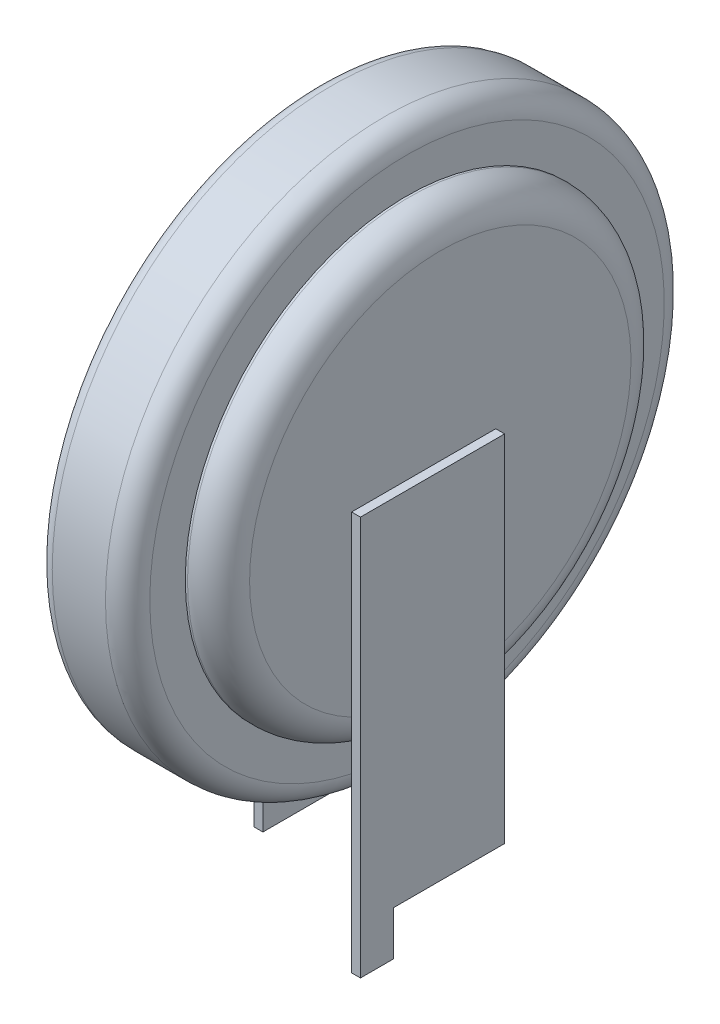
SolidWorks part; units mm, degrees
ref_plane "Front Plane" through (0, 0, 0) normal (0, 0, 1) x (1, 0, 0)
ref_plane "Top Plane" through (0, 0, 0) normal (0, 1, 0) x (1, 0, 0)
ref_plane "Right Plane" through (0, 0, 0) normal (1, 0, 0) x (0, 0, -1)
sketch "Sketch1" plane through (0, 0, 0) normal (0, 0, 1) x (1, 0, 0)
  line L0 (-11.9332, 7.8) -> (5.654, 7.8) construction
  line L1 (0, 0) -> (0, 7.8) construction
  line L2 (-1.375, 7.8) -> (1.375, 7.8)
  line L3 (1.375, 7.8) -> (1.375, 12.1)
  line L4 (0.675, 12.8) -> (0.625, 12.8)
  line L5 (0.625, 12.8) -> (0.625, 13.6)
  line L6 (0.125, 14.1) -> (-1.075, 14.1)
  line L7 (-1.375, 13.8) -> (-1.375, 7.8)
  line L8 (-3.1396, 1.5) -> (8.3283, 1.5) construction
  arc A0 (1.375, 12.1) -> (0.675, 12.8) centre (0.675, 12.1) ccw
  arc A1 (0.125, 14.1) -> (0.625, 13.6) centre (0.125, 13.6) cw
  arc A2 (-1.375, 13.8) -> (-1.075, 14.1) centre (-1.075, 13.8) cw
  point P13 (1.375, 12.8)
  dimension "D5" = 0.7
  dimension "D6" = 0.5
  dimension "D7" = 0.3
  dimension "D1" = 6.3
  dimension "D2" = 2.75
  dimension "D3" = 5
  dimension "D4" = 0.75
  dimension "D8" = 6.3
  dimension "D9" = 1.5
revolve "Revolve1" add sketch "Sketch1" angle 360 about L0
sketch "Sketch3" plane through (1.375, 0, 0) normal (1, 0, 0) x (0, 0, -1)
  line L0 (-2, 8) -> (-2, -1)
  line L1 (-2, -1) -> (-1.25, -1)
  line L2 (-1.25, -1) -> (-1.25, 0)
  line L3 (-1.25, 0) -> (1.25, 0)
  line L4 (1.25, 0) -> (1.25, 8)
  line L5 (1.25, 8) -> (-2, 8)
  line L7 (-1.625, -1) -> (-1.625, -4.628) construction
  dimension "D1" = 0.75
  dimension "D2" = 1.625
  dimension "D3" = 1
  dimension "D4" = 8
sketch "Sketch5" plane through (-1.375, 0, -1.375) normal (1, 0, 0) x (0, 0, -1)
  line L0 (-3.375, 8) -> (-3.375, -1) construction
  line L1 (-3.375, -1) -> (-2.625, -1) construction
  line L2 (-2.625, -1) -> (-2.625, 0) construction
  line L3 (-2.625, 0) -> (-0.125, 0) construction
  line L4 (-0.125, 0) -> (-0.125, 8) construction
  line L5 (-0.125, 8) -> (-3.375, 8) construction
  line L6 (0.25, -1) -> (0.25, -1.9072) construction
  line L7 (-3, -1) -> (-3, -4.628) construction
  line L8 (-3.375, 8) -> (-3.375, -1) construction
  line L9 (-3.375, -1) -> (-2.625, -1) construction
  line L10 (0.625, -1) -> (0.625, 8)
  line L11 (0.625, 8) -> (-2.625, 8)
  line L12 (-2.625, 8) -> (-2.625, 0)
  line L13 (-2.625, 0) -> (-0.125, 0)
  line L14 (-0.125, 0) -> (-0.125, -1)
  line L15 (-0.125, -1) -> (0.625, -1)
  dimension "D1" = 0.75
  dimension "D2" = 3.25
  dimension "D4" = 8
  dimension "D5" = 1
extrude "Boss-Extrude2" add sketch "Sketch3" along normal blind 0.2
extrude "Boss-Extrude3" add sketch "Sketch5" against normal blind 0.2
